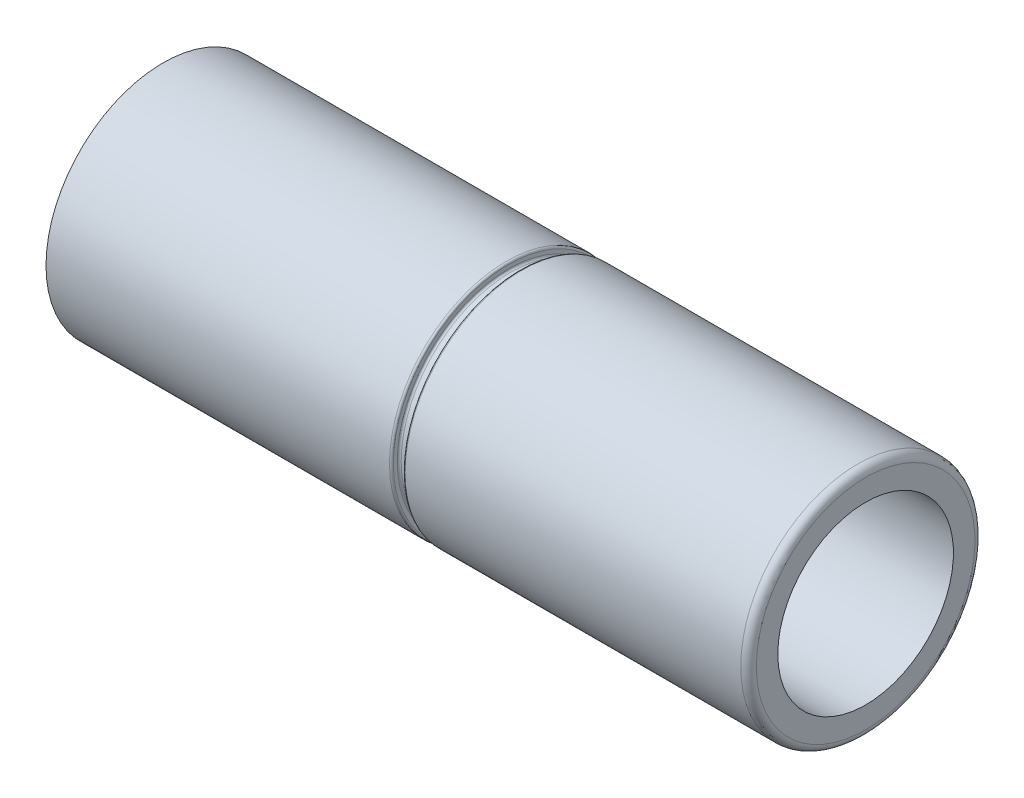
SolidWorks part; units mm, degrees
ref_plane "Front Plane" through (0, 0, 0) normal (0, 0, 1) x (1, 0, 0)
ref_plane "Top Plane" through (0, 0, 0) normal (0, 1, 0) x (1, 0, 0)
ref_plane "Right Plane" through (0, 0, 0) normal (1, 0, 0) x (0, 0, -1)
sketch "Sketch2" plane through (0, 0, 0) normal (0, 1, 0) x (1, 0, 0)
  line L0 (0, 0) -> (18, 0) construction
  line L1 (18, 2.25) -> (18, 3)
  line L2 (18, 3) -> (9.2, 3)
  line L3 (0, 3) -> (0, 2.25)
  line L4 (0, 2.25) -> (18, 2.25)
  line L5 (8.85, 2.95) -> (8.85, 2.85)
  line L6 (8.9, 2.8) -> (9.1, 2.8)
  line L7 (9.15, 2.85) -> (9.15, 2.95)
  line L8 (8.8, 3) -> (0, 3)
  arc A0 (8.85, 2.95) -> (8.8, 3) centre (8.8, 2.95) ccw
  arc A1 (9.2, 3) -> (9.15, 2.95) centre (9.2, 2.95) ccw
  arc A2 (9.1, 2.8) -> (9.15, 2.85) centre (9.1, 2.85) ccw
  arc A3 (8.9, 2.8) -> (8.85, 2.85) centre (8.9, 2.85) cw
  point P10 (9, 2.8)
  point P12 (9, 2.25)
  point P15 (8.85, 3)
  point P22 (8.85, 2.8)
  dimension "D6" = 0.05
  dimension "D1" = 18
  dimension "D2" = 0.75
  dimension "D3" = 3
  dimension "D4" = 18
  dimension "D5" = 0.2
  dimension "D7" = 0.2
revolve "Revolve1" add sketch "Sketch2" angle 360 about L0
fillet "Fillet2" radius 0.2 1 edges at (18, 0, 3)
